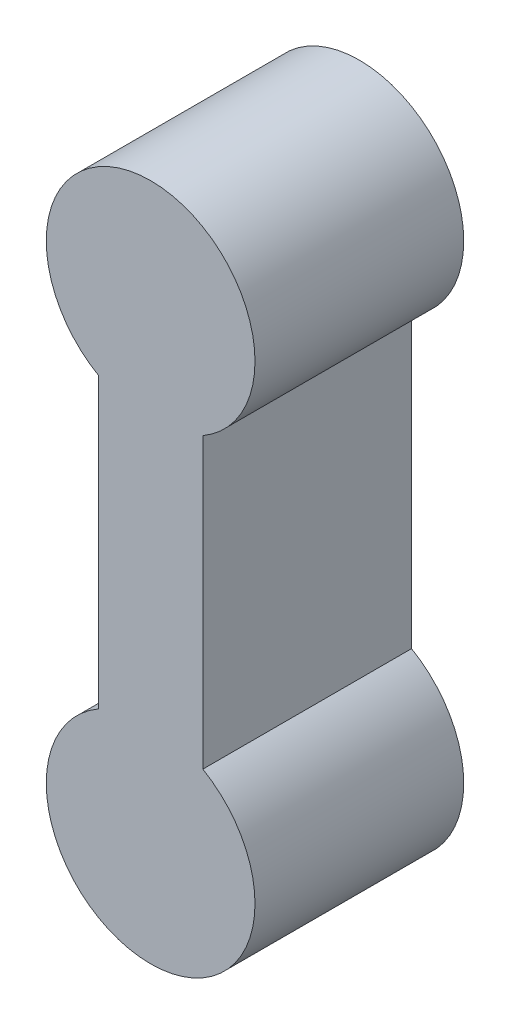
SolidWorks part; units mm, degrees
ref_plane "前视基准面" through (0, 0, 0) normal (0, 0, 1) x (1, 0, 0)
ref_plane "上视基准面" through (0, 0, 0) normal (0, 1, 0) x (1, 0, 0)
ref_plane "右视基准面" through (0, 0, 0) normal (1, 0, 0) x (0, 0, -1)
other "Configuration Table"
sketch "草图1" plane through (0, 0, 0) normal (0, 0, 1) x (1, 0, 0)
  line L0 (0, -90.6244) -> (0, 4440.5967) construction
  line L1 (-90.6244, 0) -> (4440.5967, 0) construction
  line L2 (-0.5, -1.384) -> (-0.5, 1.384)
  line L3 (0.5, -1.384) -> (0.5, 1.384)
  arc A0 (0.5, 1.384) -> (-0.5, 1.384) centre (0, 2.25) ccw
  arc A1 (0.5, -1.384) -> (-0.5, -1.384) centre (0, -2.25) cw
  point P12 (0.5, 0)
  point P13 (-0.5, 0)
  dimension "D1" = 2
  dimension "D2" = 2.25
  dimension "D3" = 1
extrude "凸台-拉伸1" add sketch "草图1" along normal blind 2
